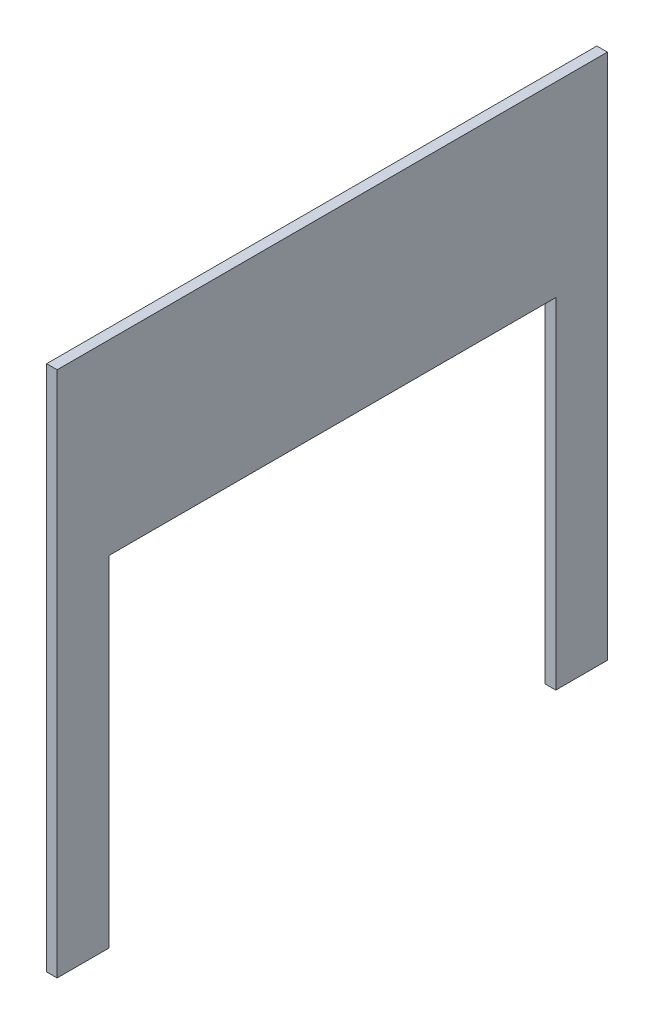
SolidWorks part; units mm, degrees
material "PVC Rigid"
ref_plane "Front Plane" through (0, 0, 0) normal (0, 0, 1) x (1, 0, 0)
ref_plane "Top Plane" through (0, 0, 0) normal (0, 1, 0) x (1, 0, 0)
ref_plane "Right Plane" through (0, 0, 0) normal (1, 0, 0) x (0, 0, -1)
sketch "Sketch1" plane through (0, 0, 0) normal (1, 0, 0) x (0, 0, -1)
  line L1 (0, 0) -> (522.3, 0)
  line L2 (0, 0) -> (0, 500)
  line L3 (0, 500) -> (522.3, 500)
  line L4 (522.3, 0) -> (522.3, 500)
  dimension "D1" = 522.3
  dimension "D2" = 500
extrude "Boss-Extrude1" add sketch "Sketch1" along normal blind 10
sketch "Sketch2" plane through (0, 0, 0) normal (-1, 0, 0) x (0, 0, 1)
  line L0 (0, 322.7) -> (-522.3, 322.7) construction
  line L1 (0, 500) -> (0, 0) construction
  line L2 (-522.3, 0) -> (-522.3, 500) construction
  line L3 (0, 0) -> (-522.3, 0) construction
  line L5 (-473.3, 0) -> (-49, 0)
  line L6 (-473.3, 0) -> (-473.3, 322.7)
  line L7 (-473.3, 322.7) -> (-49, 322.7)
  line L8 (-49, 0) -> (-49, 322.7)
  dimension "D1" = 322.7
  dimension "D2" = 49
  dimension "D3" = 49
  dimension "D4" = 322.7
extrude "Cut-Extrude1" cut sketch "Sketch2" against normal blind 10
